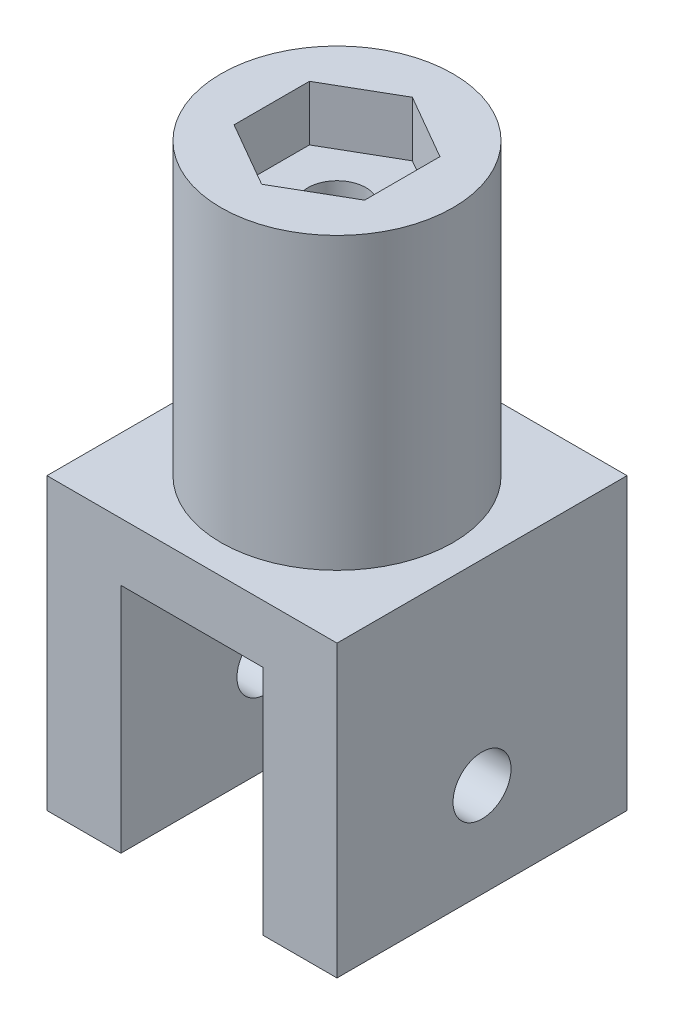
SolidWorks part; units mm, degrees
ref_plane "Front Plane" through (0, 0, 0) normal (0, 0, 1) x (1, 0, 0)
ref_plane "Top Plane" through (0, 0, 0) normal (0, 1, 0) x (1, 0, 0)
ref_plane "Right Plane" through (0, 0, 0) normal (1, 0, 0) x (0, 0, -1)
sketch "Sketch1" plane through (0, 0, 0) normal (0, 1, 0) x (1, 0, 0)
  circle A0 centre (0, 0) radius 6.5
  circle A2 centre (0, 0) radius 2
  dimension "D1" = 13
  dimension "D2" = 4
extrude "Boss-Extrude1" add sketch "Sketch1" along normal blind 20
sketch "Sketch6" plane through (0, 0, 0) normal (0, -1, 0) x (1, 0, 0)
  line L0 (0, 0) -> (10, 0) construction
  line L5 (0, 0) -> (-10, 0) construction
  line L6 (0, 0) -> (0, 10) construction
  line L7 (0, 0) -> (0, -10) construction
  line L9 (-10, 10) -> (-10, -10)
  line L10 (-10, -10) -> (10, -10)
  line L11 (10, -10) -> (10, 10)
  line L13 (-10, 10) -> (10, 10)
  dimension "D1" = 20
extrude "Boss-Extrude2" add sketch "Sketch6" along normal blind 4
sketch "Sketch7" plane through (0, 0, 10) normal (0, 0, 1) x (1, 0, 0)
  line L0 (-10, -4) -> (-10, 0) construction
  line L1 (10, 0) -> (4.9, 0)
  line L2 (10, 0) -> (10, -20)
  line L3 (10, -20) -> (4.9, -20)
  line L4 (4.9, 0) -> (4.9, -20)
  line L5 (-10, 0) -> (-4.9, 0)
  line L6 (-10, 0) -> (-10, -20)
  line L7 (-10, -20) -> (-4.9, -20)
  line L8 (-4.9, 0) -> (-4.9, -20)
  line L9 (10, 0) -> (-10, 0) construction
  dimension "D1" = 9.8
  dimension "D2" = 20
extrude "Boss-Extrude3" add sketch "Sketch7" against normal up to surface (20 mm away) up to face at (0, -2, -10)
sketch "Sketch8" plane through (10, 0, 0) normal (1, 0, 0) x (0, 0, -1)
  line L0 (10, -13.5) -> (-10, -13.5) construction
  line L1 (10, -20) -> (10, 0) construction
  line L2 (-10, -20) -> (-10, 0) construction
  line L3 (10, -20) -> (-10, -20) construction
  circle A0 centre (0, -13.5) radius 2
  dimension "D2" = 4
  dimension "D1" = 6.5
extrude "Cut-Extrude1" cut sketch "Sketch8" against normal through all
sketch "Sketch14" plane through (0, 0, 0) normal (0, 1, 0) x (1, 0, 0)
  circle A0 centre (0, 0) radius 8
  circle A1 centre (0, 0) radius 6.5
  dimension "D1" = 16
  dimension "D2" = 13
extrude "Boss-Extrude4" add sketch "Sketch14" along normal up to surface (20 mm away) up to face at (0, 20, 6.5)
sketch "Sketch15" plane through (0, 20, 0) normal (0, 1, 0) x (1, 0, 0)
  line L0 (0, 8) -> (0, -8) construction
  line L1 (-8, 0) -> (8, 0) construction
  line L3 (4.5, 2.5981) -> (0, 5.1962)
  line L4 (0, 5.1962) -> (-4.5, 2.5981)
  line L5 (-4.5, 2.5981) -> (-4.5, -2.5981)
  line L6 (-4.5, -2.5981) -> (0, -5.1962)
  line L7 (0, -5.1962) -> (4.5, -2.5981)
  line L8 (4.5, -2.5981) -> (4.5, 2.5981)
  circle A0 centre (0, 0) radius 8 construction
  circle A1 centre (0, 0) radius 4.5 construction
  point P8 (0, 6.7767)
  point P16 (4.8711, 2.8123)
  dimension "D1" = 9
extrude "Cut-Extrude2" cut sketch "Sketch15" against normal blind 3.8
